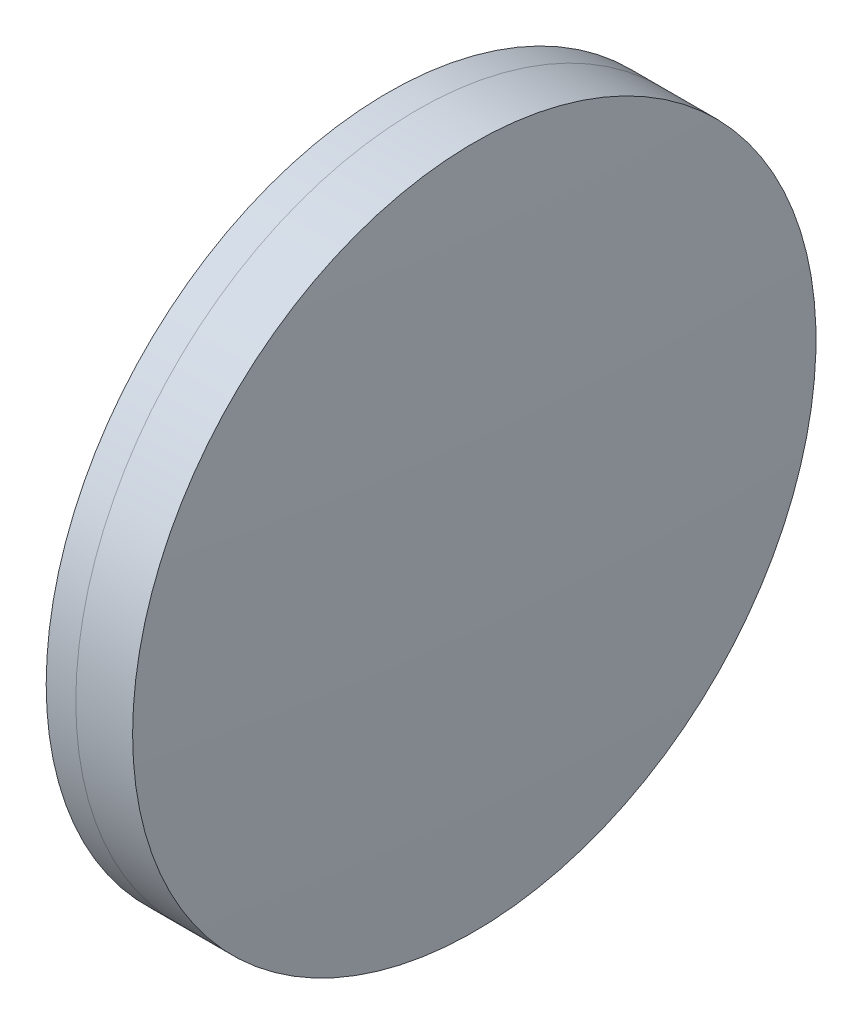
SolidWorks part; units mm, degrees
ref_plane "前视基准面" through (0, 0, 0) normal (0, 0, 1) x (1, 0, 0)
ref_plane "上视基准面" through (0, 0, 0) normal (0, 1, 0) x (1, 0, 0)
ref_plane "右视基准面" through (0, 0, 0) normal (1, 0, 0) x (0, 0, -1)
sketch "草图1" plane through (0, 0, 0) normal (0, 1, 0) x (1, 0, 0)
  line L0 (124.5233, 0) -> (395.1269, 0) construction
  line L1 (364.1952, -25.4) -> (366.3955, -25.4)
  line L2 (364.1952, 25.4) -> (366.3955, 25.4)
  arc A0 (366.3955, -25.4) -> (366.3955, 25.4) centre (257.6218, 0) ccw
  arc A1 (364.1952, 25.4) -> (364.1952, -25.4) centre (498.9218, 0) ccw
  point P10 (361.8218, 0)
  point P11 (369.3218, 0)
  dimension "D3" = 137.1
  dimension "D4" = 111.7
  dimension "D1" = 25.4
  dimension "D2" = 25.4
  dimension "D5" = 7.5
revolve "旋转1" add sketch "草图1" angle 360 about L0
sketch "草图2" plane through (0, 0, 0) normal (0, 1, 0) x (1, 0, 0)
  line L0 (-0.5519, 0) -> (409.4962, 0) construction
  line L2 (366.3955, 25.4) -> (370.6188, 25.4)
  line L3 (366.3955, -25.4) -> (370.6188, -25.4)
  arc A0 (370.6188, -25.4) -> (370.6188, 25.4) centre (-87.8782, 0) ccw
  arc A1 (366.3955, -25.4) -> (366.3955, 25.4) centre (257.6218, 0) ccw construction
  arc A2 (366.3955, -25.4) -> (366.3955, 25.4) centre (257.6218, 0) ccw
  point P4 (369.3218, 0)
  point P8 (371.3218, 0)
  dimension "D1" = 459.2
  dimension "D2" = 2
revolve "旋转3" add sketch "草图2" angle 360 about L0
